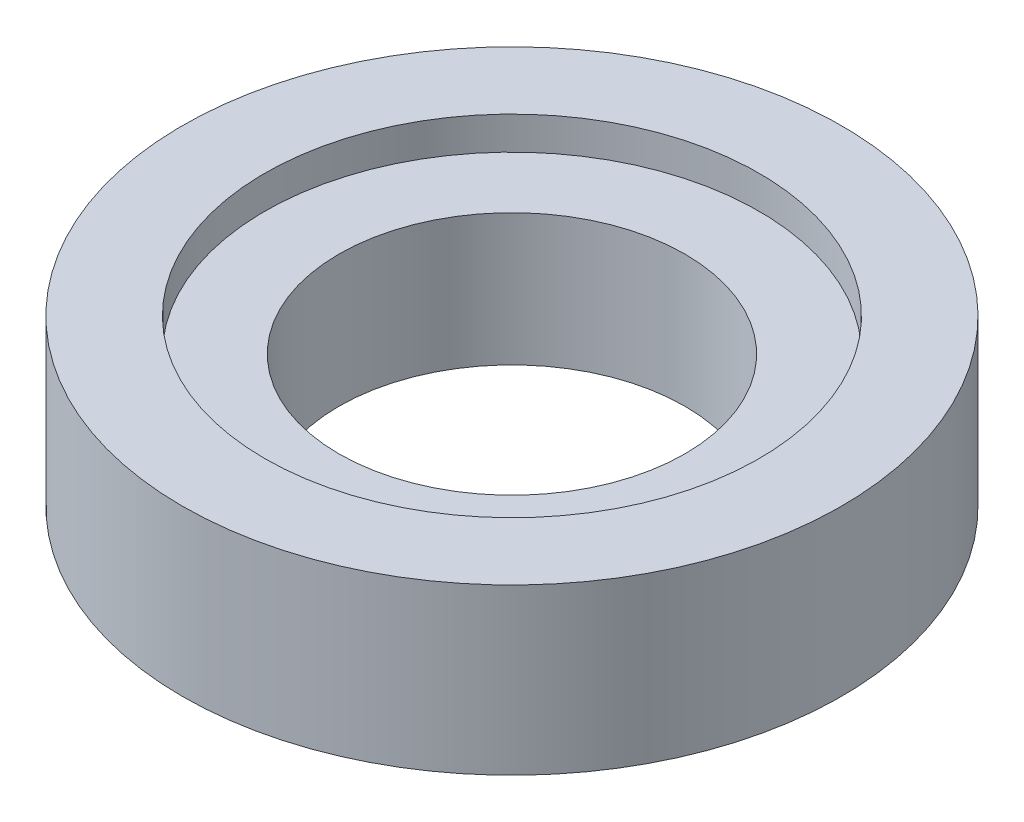
SolidWorks part; units mm, degrees
ref_plane "Plan de face" through (0, 0, 0) normal (0, 0, 1) x (1, 0, 0)
ref_plane "Plan de dessus" through (0, 0, 0) normal (0, 1, 0) x (1, 0, 0)
ref_plane "Plan de droite" through (0, 0, 0) normal (1, 0, 0) x (0, 0, -1)
sketch "Esquisse1" plane through (0, 0, 0) normal (0, 1, 0) x (1, 0, 0)
  circle A0 centre (0, 0) radius 10
  circle A1 centre (0, 0) radius 5.25
  dimension "D1" = 20
  dimension "D2" = 10.5
extrude "Boss.-Extru.1" add sketch "Esquisse1" along normal blind 5
sketch "Esquisse2" plane through (0, 5, 0) normal (0, 1, 0) x (1, 0, 0)
  circle A0 centre (0, 0) radius 7.5
  dimension "D1" = 15
extrude "Enlèv. mat.-Extru.1" cut sketch "Esquisse2" against normal blind 1
